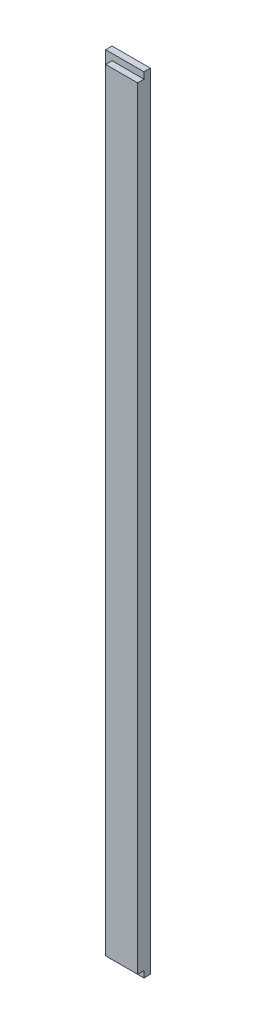
SolidWorks part; units mm, degrees
ref_plane "Front Plane" through (0, 0, 0) normal (0, 0, 1) x (1, 0, 0)
ref_plane "Top Plane" through (0, 0, 0) normal (0, 1, 0) x (1, 0, 0)
ref_plane "Right Plane" through (0, 0, 0) normal (1, 0, 0) x (0, 0, -1)
sketch "Sketch1" plane through (0, 0, 0) normal (0, 0, 1) x (1, 0, 0)
  line L0 (-30, 615) -> (30, 615)
  line L1 (30, 615) -> (30, -615)
  line L2 (30, -615) -> (-30, -615)
  line L3 (-30, -615) -> (-30, 615)
  point P2 (0, 615)
  point P5 (-30, 0)
  dimension "D1" = 60
  dimension "D2" = 1230
extrude "Boss-Extrude1" add sketch "Sketch1" along normal blind 20
sketch "Sketch2" plane through (0, 0, 20) normal (0, 0, 1) x (1, 0, 0)
  line L0 (30, 605) -> (-20, 605)
  line L1 (-20, 605) -> (-20, -605)
  line L2 (-20, -605) -> (30, -605)
  line L4 (-30, 615) -> (-30, -615)
  line L5 (-30, -615) -> (30, -615)
  line L6 (30, -615) -> (30, 615)
  line L7 (30, 615) -> (-30, 615)
  line L8 (-30, 615) -> (-30, -615)
  line L9 (-30, -615) -> (30, -615)
  line L10 (30, -615) -> (30, -605)
  line L11 (30, 615) -> (-30, 615)
  line L12 (20, -605) -> (20, 605) construction
  line L13 (20, 605) -> (-20, 605) construction
  line L14 (-20, -605) -> (20, -605) construction
  line L15 (30, 605) -> (30, 615)
  line L16 (30, -615) -> (30, 615) construction
  dimension "D1" = 0
  dimension "D2" = 10
extrude "Cut-Extrude1" cut sketch "Sketch2" against normal blind 10
